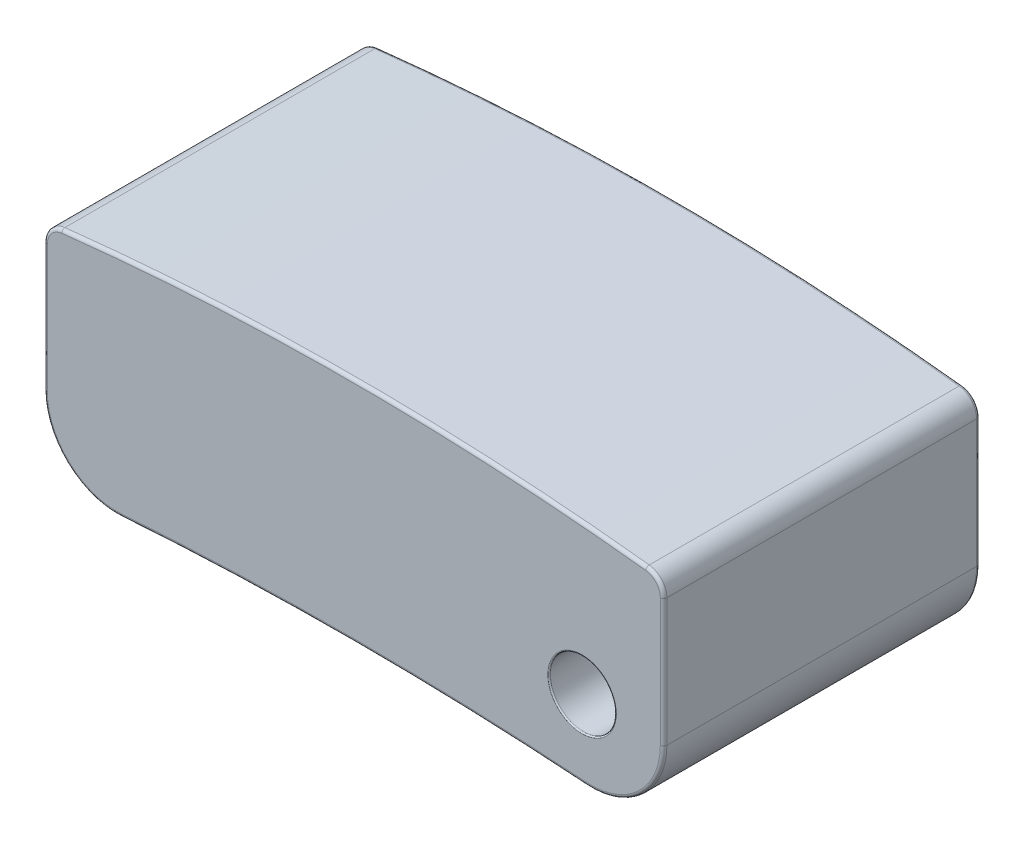
SolidWorks part; units mm, degrees
ref_plane "Front Plane" through (0, 0, 0) normal (0, 0, 1) x (1, 0, 0)
ref_plane "Top Plane" through (0, 0, 0) normal (0, 1, 0) x (1, 0, 0)
ref_plane "Right Plane" through (0, 0, 0) normal (1, 0, 0) x (0, 0, -1)
sketch "Sketch1" plane through (0, 0, 0) normal (0, 0, 1) x (1, 0, 0)
  line L0 (55, 0) -> (-55, 0) construction
  line L1 (-4.7, 1.85) -> (4.7, 1.85)
  line L2 (-4.7, 1.85) -> (-4.7, -1.85)
  line L3 (-4.7, -1.85) -> (4.7, -1.85)
  line L4 (4.7, 1.85) -> (4.7, -1.85)
  line L5 (0, -55) -> (0, 55) construction
  dimension "D1" = 9.4
  dimension "D2" = 3.7
  dimension "D3" = 1.85
  dimension "D4" = 4.7
extrude "Boss-Extrude1" add sketch "Sketch1" along normal mid plane 4.8
sketch "Sketch2" plane through (0, 0, 2.4) normal (0, 0, 1) x (1, 0, 0)
  line L0 (-4.7, 1.85) -> (-4.7, -1.85) construction
  line L1 (4.7, -1.85) -> (4.7, 1.85) construction
  line L2 (-4.7, -1.85) -> (4.7, -1.85) construction
  line L3 (4.7, 1.85) -> (-4.7, 1.85) construction
  line L4 (-4.7, 1.55) -> (-7.1207, 4.0114)
  line L5 (-7.1207, 4.0114) -> (5.5359, 3.8867)
  line L6 (5.5359, 3.8867) -> (4.7, 1.55)
  line L7 (4.7, -1.85) -> (0.3506, -3.782)
  line L8 (-4.7, -1.85) -> (0.3506, -3.782)
  arc A0 (-4.7, 1.55) -> (4.7, 1.55) centre (0, -38.1729) cw
  arc A1 (-4.7, -1.85) -> (4.7, -1.85) centre (0, -51.6286) cw
  dimension "D4" = 40
  dimension "D5" = 50
  dimension "D1" = 0
  dimension "D2" = 0.3
  dimension "D3" = 0.3
extrude "Cut-Extrude1" cut sketch "Sketch2" against normal blind 4.8
fillet "Fillet1" radius 1.1 2 edges at (4.7, -1.85, 0) (-4.7, -1.85, 0)
fillet "Fillet2" radius 0.3 2 edges at (4.7, 1.55, 0) (-4.7, 1.55, 0)
fillet "Fillet3" radius 0.05 16 edges at (-4.6236, 1.4825, -2.4) (-4.7, 0.3135, -2.4) (-4.3499, -1.4603, -2.4) (0, -1.6286, -2.4) (4.3499, -1.4603, -2.4) (4.7, 0.3135, -2.4) (4.6236, 1.4825, -2.4) (0, 1.8271, -2.4) (4.3499, -1.4603, 2.4) (0, -1.6286, 2.4) (-4.3499, -1.4603, 2.4) (-4.7, 0.3135, 2.4) (-4.6236, 1.4825, 2.4) (0, 1.8271, 2.4) (4.6236, 1.4825, 2.4) (4.7, 0.3135, 2.4)
sketch "Sketch3" plane through (0, 0, 2.4) normal (0, 0, 1) x (1, 0, 0)
  circle A0 centre (3.4626, -0.5787) radius 0.5
  dimension "D1" = 1
extrude "Cut-Extrude2" cut sketch "Sketch3" against normal blind 4.8
fillet "Fillet4" radius 0.02 2 edges at (3.9626, -0.5787, -2.4) (3.9626, -0.5787, 2.4)
mirror "Mirror1" about plane through (0, 0, 0) normal (1, 0, 0) of "Cut-Extrude2"
sketch "Sketch4" plane through (0, 0, 2.4) normal (0, 0, 1) x (1, 0, 0)
  line L1 (-4.2939, 0) -> (-2.4123, 0)
  line L2 (-4.2939, 0) -> (-4.2939, -1.1776)
  line L3 (-4.2939, -1.1776) -> (-2.4123, -1.1776)
  line L4 (-2.4123, 0) -> (-2.4123, -1.1776)
extrude "Boss-Extrude2" add sketch "Sketch4" against normal blind 1
sketch "Sketch5" plane through (0, 0, 1.4) normal (0, 0, -1) x (-1, 0, 0)
  circle A1 centre (3.4626, -0.5787) radius 0.5
  circle A2 centre (3.4626, -0.5787) radius 0.5
  dimension "D1" = 0
extrude "Cut-Extrude3" cut sketch "Sketch5" against normal blind 10
sketch "Sketch6" plane through (0, 0, 2.4) normal (0, 0, 1) x (1, 0, 0)
  circle A0 centre (-3.4326, -0.5004) radius 0.8678
extrude "Boss-Extrude3" add sketch "Sketch6" against normal blind 1
sketch "Sketch7" plane through (0, 0, 0) normal (0, 1, 0) x (1, 0, 0)
  line L0 (-4.7, 2.35) -> (-4.7, -2.35) construction
  line L1 (3.526, 2.4) -> (-3.526, 2.4) construction
  circle A0 centre (-0.7, 0.9) radius 0.4
  dimension "D1" = 4
  dimension "D2" = 0.8
  dimension "D3" = 1.5
extrude "Cut-Extrude4" cut sketch "Sketch7" along normal offset from surface (8.7665 mm away) 0.4 from offset 10 offset against normal yes
fillet "Fillet5" radius 0.05 1 edges at (-0.792, -1.6349, -0.5107)
